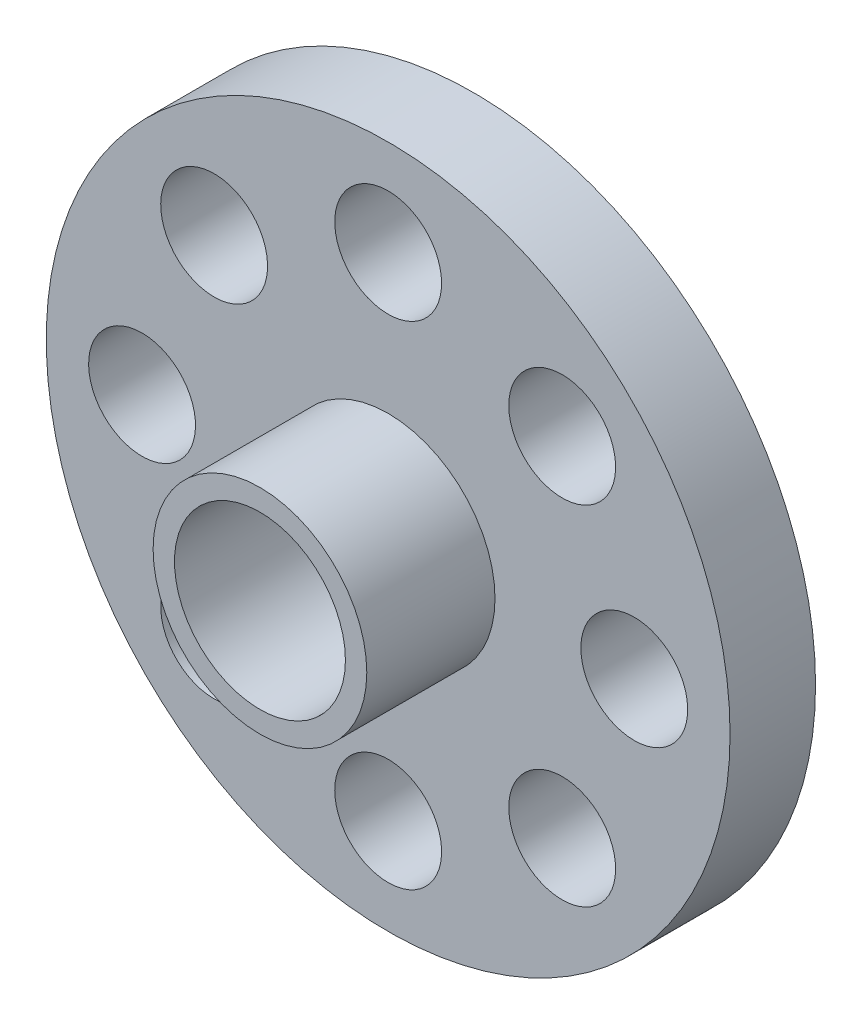
SolidWorks part; units mm, degrees
ref_plane "前视基准面" through (0, 0, 0) normal (0, 0, 1) x (1, 0, 0)
ref_plane "上视基准面" through (0, 0, 0) normal (0, 1, 0) x (1, 0, 0)
ref_plane "右视基准面" through (0, 0, 0) normal (1, 0, 0) x (0, 0, -1)
sketch "草图1" plane through (0, 0, 0) normal (0, 0, 1) x (1, 0, 0)
  circle A0 centre (0, 0) radius 16
  circle A1 centre (0, 0) radius 4
extrude "凸台-拉伸2" add sketch "草图1" along normal blind 10
sketch "草图3" plane through (0, 0, 10) normal (0, 0, 1) x (1, 0, 0)
  circle A0 centre (0, 0) radius 5
  circle A1 centre (0, 0) radius 16
extrude "切除-拉伸2" cut sketch "草图3" against normal blind 6
sketch "草图4" plane through (0, 0, 4) normal (0, 0, 1) x (1, 0, 0)
  circle A0 centre (0, 11.5168) radius 2.5
extrude "切除-拉伸3" cut sketch "草图4" against normal through all
pattern_circular "阵列(圆周)1" count 8 over 360 about axis through (0, 0, 0) along (0, 0, 1) of "切除-拉伸3"
